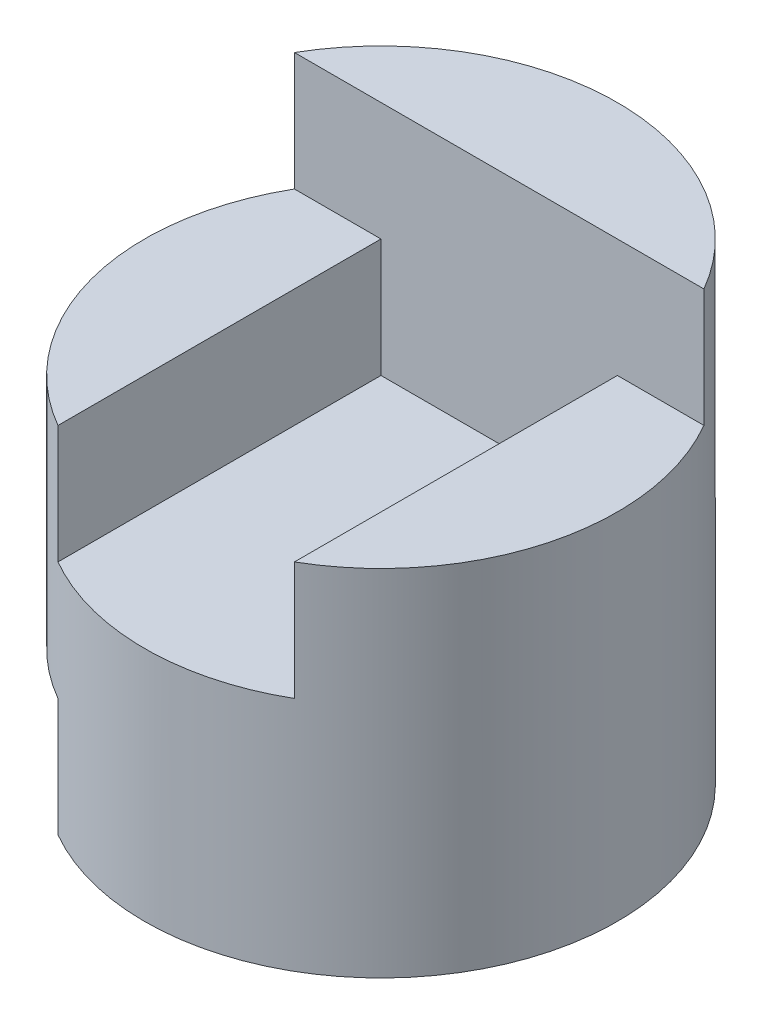
SolidWorks part; units mm, degrees
ref_plane "Front" through (0, 0, 0) normal (0, 0, 1) x (1, 0, 0)
ref_plane "Top" through (0, 0, 0) normal (0, 1, 0) x (1, 0, 0)
ref_plane "Right" through (0, 0, 0) normal (1, 0, 0) x (0, 0, -1)
sketch "Sketch1" plane through (0, 0, 0) normal (0, 1, 0) x (1, 0, 0)
  circle A0 centre (0, 0) radius 2
  dimension "D1" = 4
extrude "Boss-Extrude1" add sketch "Sketch1" along normal blind 4
sketch "Sketch2" plane through (0, 0, 0) normal (0, 0, 1) x (1, 0, 0)
  line L0 (-2, 4) -> (2, 4)
  line L1 (2, 4) -> (2, 3)
  line L2 (2, 0) -> (2, 4) construction
  line L3 (2, 3) -> (1, 3)
  line L4 (1, 3) -> (1, 2)
  line L5 (1, 2) -> (-1, 2)
  line L6 (-1, 2) -> (-1, 3)
  line L7 (-1, 3) -> (-2, 3)
  line L8 (-2, 3) -> (-2, 4)
  dimension "D1" = 1
  dimension "D2" = 1
  dimension "D3" = 1
  dimension "D4" = 1
  dimension "D5" = 1
extrude "Cut-Extrude1" cut sketch "Sketch2" against normal blind 1 and the other way blind 3
sketch "Sketch4" plane through (0, 0, 0) normal (0, -1, 0) x (1, 0, 0)
  line L0 (-1, 1.7321) -> (-1, -1)
  line L1 (-1, -1) -> (-1.7321, -1)
  arc A0 (-1.7321, -1) -> (-1, 1.7321) centre (0, 0) cw
extrude "Cut-Extrude9" cut sketch "Sketch4" against normal blind 1
